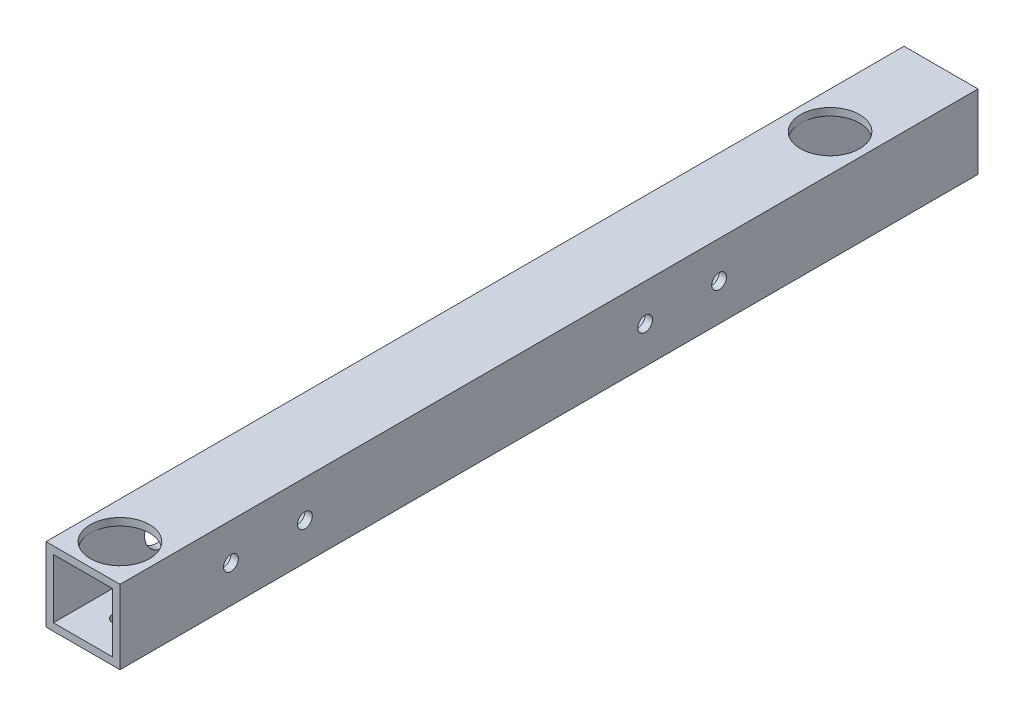
SolidWorks part; units mm, degrees
material "1060 合金"
ref_plane "正面" through (0, 0, 0) normal (0, 0, 1) x (1, 0, 0)
ref_plane "平面" through (0, 0, 0) normal (0, 1, 0) x (1, 0, 0)
ref_plane "右側面" through (0, 0, 0) normal (1, 0, 0) x (0, 0, -1)
sketch "ｽｹｯﾁ1" plane through (0, 0, 0) normal (0, 0, 1) x (1, 0, 0)
  line L1 (-7.0101, 7.7326) -> (7.9899, 7.7326)
  line L2 (-7.0101, 7.7326) -> (-7.0101, -7.2674)
  line L3 (-7.0101, -7.2674) -> (7.9899, -7.2674)
  line L4 (7.9899, 7.7326) -> (7.9899, -7.2674)
  line L9 (-5.5101, 6.2326) -> (6.4899, 6.2326)
  line L10 (-5.5101, 6.2326) -> (-5.5101, -5.7674)
  line L11 (-5.5101, -5.7674) -> (6.4899, -5.7674)
  line L12 (6.4899, 6.2326) -> (6.4899, -5.7674)
  dimension "D1" = 15
  dimension "D2" = 15
  dimension "D3" = 1.5
  dimension "D4" = 1.5
  dimension "D5" = 12
  dimension "D6" = 12
extrude "ﾎﾞｽ - 押し出し2" add sketch "ｽｹｯﾁ1" along normal blind 174
sketch "ｽｹｯﾁ2" plane through (0, -7.2674, 0) normal (0, -1, 0) x (-1, 0, 0)
  line L1 (7.0101, 0) -> (-0.4899, 0)
  line L2 (7.0101, 0) -> (7.0101, -7.5)
  line L3 (7.0101, -7.5) -> (-0.4899, -7.5)
  line L4 (-0.4899, 0) -> (-0.4899, -7.5)
  circle A0 centre (-0.4899, -7.5) radius 1.5
  dimension "D3" = 3
  dimension "D1" = 7.5
  dimension "D2" = 7.5
extrude "ｶｯﾄ - 押し出し1" cut sketch "ｽｹｯﾁ2" against normal blind 10 contours L4 A0 L3 | L3 A0 L4
sketch "ｽｹｯﾁ3" plane through (7.9899, 0, 0) normal (1, 0, 0) x (0, 0, -1)
  line L0 (0, 0.2326) -> (-52.5, 0.2326)
  line L1 (0, -7.2674) -> (0, 7.7326) construction
  circle A0 centre (-52.5, 0.2326) radius 1.5
  dimension "D2" = 3
  dimension "D1" = 52.5
extrude "ｶｯﾄ - 押し出し2" cut sketch "ｽｹｯﾁ3" against normal blind 10
sketch "ｽｹｯﾁ6" plane through (-7.0101, 0, 0) normal (-1, 0, 0) x (0, 0, 1)
  line L0 (0, 0.2326) -> (52.5, 0.2326)
  line L1 (0, 7.7326) -> (0, -7.2674) construction
  circle A0 centre (52.5, 0.2326) radius 4
  dimension "D1" = 52.5
extrude "ｶｯﾄ - 押し出し4" cut sketch "ｽｹｯﾁ6" against normal blind 10
sketch "ｽｹｯﾁ7" plane through (7.9899, 0, 0) normal (1, 0, 0) x (0, 0, -1)
  line L0 (-174, 0.2326) -> (-151.5, 0.2326)
  line L1 (-174, -7.2674) -> (-174, 7.7326) construction
  circle A0 centre (-151.5, 0.2326) radius 1.5
  dimension "D1" = 22.5
extrude "ｶｯﾄ - 押し出し5" cut sketch "ｽｹｯﾁ7" against normal blind 10
sketch "ｽｹｯﾁ8" plane through (-7.0101, 0, 0) normal (-1, 0, 0) x (0, 0, 1)
  line L0 (174, 0.2326) -> (151.5, 0.2326)
  line L1 (174, 7.7326) -> (174, -7.2674) construction
  circle A0 centre (151.5, 0.2326) radius 4
  dimension "D1" = 22.5
extrude "ｶｯﾄ - 押し出し6" cut sketch "ｽｹｯﾁ8" against normal blind 10
sketch "ｽｹｯﾁ10" plane through (-7.0101, 0, 0) normal (-1, 0, 0) x (0, 0, 1)
  line L0 (0, 0.2326) -> (86.8, 0.2326)
  line L1 (0, 7.7326) -> (0, -7.2674) construction
  circle A0 centre (86.8, 0.2326) radius 1.5
  dimension "D2" = 3
  dimension "D1" = 86.8
extrude "ｶｯﾄ - 押し出し9" cut sketch "ｽｹｯﾁ10" against normal blind 10
sketch "ｽｹｯﾁ12" plane through (0, -7.2674, 0) normal (0, -1, 0) x (1, 0, 0)
  line L0 (0.4899, 0) -> (0.4899, 86.8)
  line L1 (-7.0101, 0) -> (7.9899, 0) construction
  circle A0 centre (0.4899, 86.8) radius 4
  dimension "D1" = 86.8
extrude "ｶｯﾄ - 押し出し10" cut sketch "ｽｹｯﾁ12" against normal blind 10
sketch "ｽｹｯﾁ13" plane through (-7.0101, 0, 0) normal (-1, 0, 0) x (0, 0, 1)
  line L0 (86.8, 0.2326) -> (116.8, 0.2326)
  circle A0 centre (116.8, 0.2326) radius 1.5
  dimension "D1" = 30
extrude "ｶｯﾄ - 押し出し11" cut sketch "ｽｹｯﾁ13" against normal blind 10
sketch "ｽｹｯﾁ14" plane through (0, -7.2674, 0) normal (0, -1, 0) x (1, 0, 0)
  line L0 (0.4899, 86.8) -> (0.4899, 116.8)
  circle A0 centre (0.4899, 116.8) radius 4
  dimension "D1" = 30
extrude "ｶｯﾄ - 押し出し12" cut sketch "ｽｹｯﾁ14" against normal blind 10
sketch "ｽｹｯﾁ15" plane through (0, -7.2674, 0) normal (0, -1, 0) x (1, 0, 0)
  line L0 (0.4899, 7.5) -> (0.4899, 22.5)
  circle A0 centre (0.4899, 22.5) radius 1.5
  dimension "D1" = 15
extrude "ｶｯﾄ - 押し出し13" cut sketch "ｽｹｯﾁ15" against normal blind 10
sketch "ｽｹｯﾁ16" plane through (0, 7.7326, 0) normal (0, 1, 0) x (1, 0, 0)
  line L0 (0.4899, 0) -> (0.4899, -22.5)
  line L1 (7.9899, 0) -> (-7.0101, 0) construction
  circle A0 centre (0.4899, -22.5) radius 6
  dimension "D1" = 22.5
extrude "ｶｯﾄ - 押し出し14" cut sketch "ｽｹｯﾁ16" against normal blind 10
sketch "ｽｹｯﾁ17" plane through (0, -7.2674, 0) normal (0, -1, 0) x (1, 0, 0)
  line L0 (0.4899, 174) -> (0.4899, 166.5)
  line L1 (-7.0101, 174) -> (7.9899, 174) construction
  circle A0 centre (0.4899, 166.5) radius 1.5
  dimension "D1" = 7.5
extrude "ｶｯﾄ - 押し出し15" cut sketch "ｽｹｯﾁ17" against normal blind 10 contours A0
sketch "ｽｹｯﾁ18" plane through (0, 7.7326, 0) normal (0, 1, 0) x (1, 0, 0)
  line L0 (0.4899, -174) -> (0.4899, -166.5)
  line L1 (7.9899, -174) -> (-7.0101, -174) construction
  circle A0 centre (0.4899, -166.5) radius 6
  dimension "D1" = 7.5
extrude "ｶｯﾄ - 押し出し16" cut sketch "ｽｹｯﾁ18" against normal blind 10
sketch "ｽｹｯﾁ19" plane through (-7.0101, 0, 0) normal (-1, 0, 0) x (0, 0, 1)
  line L0 (174, -7.2674) -> (0, -7.2674) construction
  circle A0 centre (67.5, 0.2326) radius 4
  circle A1 centre (52.5, 0.2326) radius 4 construction
  dimension "D3" = 8
  dimension "D1" = 7.5
  dimension "D2" = 15
extrude "ｶｯﾄ - 押し出し17" cut sketch "ｽｹｯﾁ19" against normal blind 10
sketch "ｽｹｯﾁ20" plane through (7.9899, 0, 0) normal (1, 0, 0) x (0, 0, -1)
  line L0 (-174, 7.7326) -> (0, 7.7326) construction
  circle A0 centre (-67.5, 0.2326) radius 1.5
  circle A1 centre (-52.5, 0.2326) radius 1.5 construction
  dimension "D1" = 15
  dimension "D2" = 7.5
extrude "ｶｯﾄ - 押し出し18" cut sketch "ｽｹｯﾁ20" against normal blind 10
sketch "ｽｹｯﾁ21" plane through (7.9899, 0, 0) normal (1, 0, 0) x (0, 0, -1)
  circle A0 centre (-136.5, 0.2326) radius 1.5
  circle A1 centre (-151.5, 0.2326) radius 1.5 construction
  dimension "D1" = 15
extrude "ｶｯﾄ - 押し出し19" cut sketch "ｽｹｯﾁ21" against normal blind 10
sketch "ｽｹｯﾁ22" plane through (-7.0101, 0, 0) normal (-1, 0, 0) x (0, 0, 1)
  line L0 (174, -7.2674) -> (0, -7.2674) construction
  circle A0 centre (136.5, 0.2326) radius 4
  circle A1 centre (151.5, 0.2326) radius 4 construction
  dimension "D1" = 15
  dimension "D2" = 7.5
extrude "ｶｯﾄ - 押し出し20" cut sketch "ｽｹｯﾁ22" against normal blind 10
